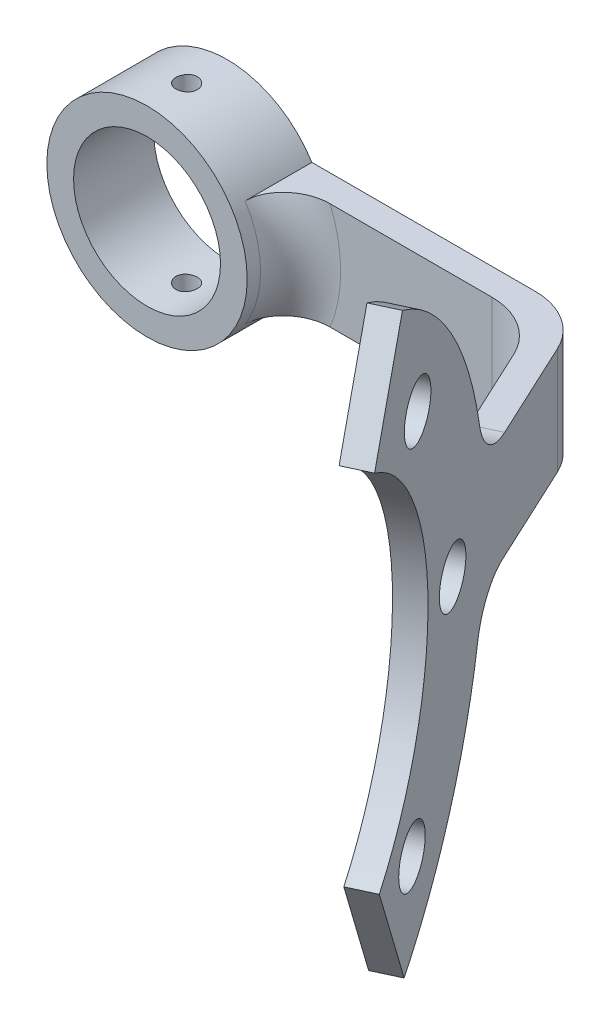
SolidWorks part; units mm, degrees
material "201 Annealed Stainless Steel (SS)"
ref_plane "Front Plane" through (0, 0, 0) normal (0, 0, 1) x (1, 0, 0)
ref_plane "Top Plane" through (0, 0, 0) normal (0, 1, 0) x (1, 0, 0)
ref_plane "Right Plane" through (0, 0, 0) normal (1, 0, 0) x (0, 0, -1)
sketch "Sketch1" plane through (0, 0, 0) normal (0, 1, 0) x (1, 0, 0)
  line L0 (0, 0) -> (0, 2)
  line L3 (34.5181, -15.688) -> (32.7602, -16.6417)
  line L6 (0, 0) -> (25, 0)
  line L7 (25, 0) -> (32.7602, -16.6417)
  line L8 (26.2701, 2) -> (34.5181, -15.688)
  line L9 (0, 2) -> (26.2701, 2)
  dimension "D1" = 2
  dimension "D2" = 2
  dimension "D3" = 115
  dimension "D4" = 25
extrude "Boss-Extrude1" add sketch "Sketch1" along normal blind 8
fillet "Fillet1" radius 5 2 edges at (26.2701, 4, -2) (25, 4, 0)
sketch "Sketch5" plane through (22.3441, 0, -10.4192) normal (0.9063, 0, -0.4226) x (-0.4226, 0, -0.9063)
  line L0 (-40.7809, 18.7361) -> (-36.4672, 26.4289)
  line L1 (-40.0493, -9.0573) -> (-36.2057, -17.037)
  line L2 (-32.5193, 4.1187) -> (-28.7015, 4) construction
  arc A0 (-36.2057, -17.037) -> (-36.4672, 26.4289) centre (-48.6919, 4.6216) ccw
  arc A1 (-38.3829, -12.5169) -> (-38.9127, 22.0677) centre (-48.6919, 4.6216) ccw construction
  arc A2 (-40.0493, -9.0573) -> (-40.7809, 18.7361) centre (-48.6919, 4.6216) ccw
  dimension "D5" = 25
  dimension "D1" = 125
  dimension "D2" = 62.5
extrude "Boss-Extrude2" add sketch "Sketch5" against normal blind 2 contours L1 A0 L0 A2
sketch "Sketch3" plane through (20.5348, 0, -9.5756) normal (-0.9063, 0, 0.4226) x (0.4226, 0, 0.9063)
  circle A0 centre (28.7015, 4) radius 2.05
  circle A1 centre (48.6919, 4.6216) radius 20 construction
  circle A2 centre (34.117, 18.3174) radius 2.05
  circle A3 centre (48.0703, 24.6119) radius 2.05
  circle A4 centre (62.3876, 19.1964) radius 2.05
  circle A5 centre (68.6822, 5.2431) radius 2.05
  circle A6 centre (63.2667, -9.0742) radius 2.05
  circle A7 centre (49.3134, -15.3688) radius 2.05
  circle A8 centre (34.9961, -9.9533) radius 2.05
  point P23 (48.6919, 4.6216)
  dimension "D1" = 4.1
  dimension "D3" = 8
extrude "Cut-Extrude3" cut sketch "Sketch3" against normal blind 10 and the other way blind 10
fillet "Fillet2" radius 4 2 edges at (31.6342, 0, 11.8652) (31.549, 8, 11.6826)
sketch "Sketch6" plane through (0, 0, -2) normal (0, 0, -1) x (-1, 0, 0)
  line L0 (0, 8) -> (0, 0) construction
  circle A0 centre (0, 4) radius 7.5
  dimension "D1" = 15
extrude "Boss-Extrude3" add sketch "Sketch6" against normal blind 6
sketch "Sketch2" plane through (0, 0, 0) normal (0, 0, 1) x (1, 0, 0)
  circle A2 centre (0, 4) radius 5.5
  dimension "D1" = 11
extrude "Cut-Extrude4" cut sketch "Sketch2" against normal through all and the other way through all
ref_plane "Plane1" through (0, -3.5, 0) normal (0, -1, 0) x (-1, 0, 0)
sketch "Sketch8" plane through (0, -3.5, 0) normal (0, -1, 0) x (-1, 0, 0)
  circle A0 centre (0, -1.034) radius 0.8
  dimension "D1" = 1.6
extrude "Cut-Extrude5" cut sketch "Sketch8" against normal through all contours A0
fillet "Fillet3" radius 3 1 edges at (7.5, 4, 0)
equation "\"D2@Sketch5\"=\"D1@Sketch5\"/2"
